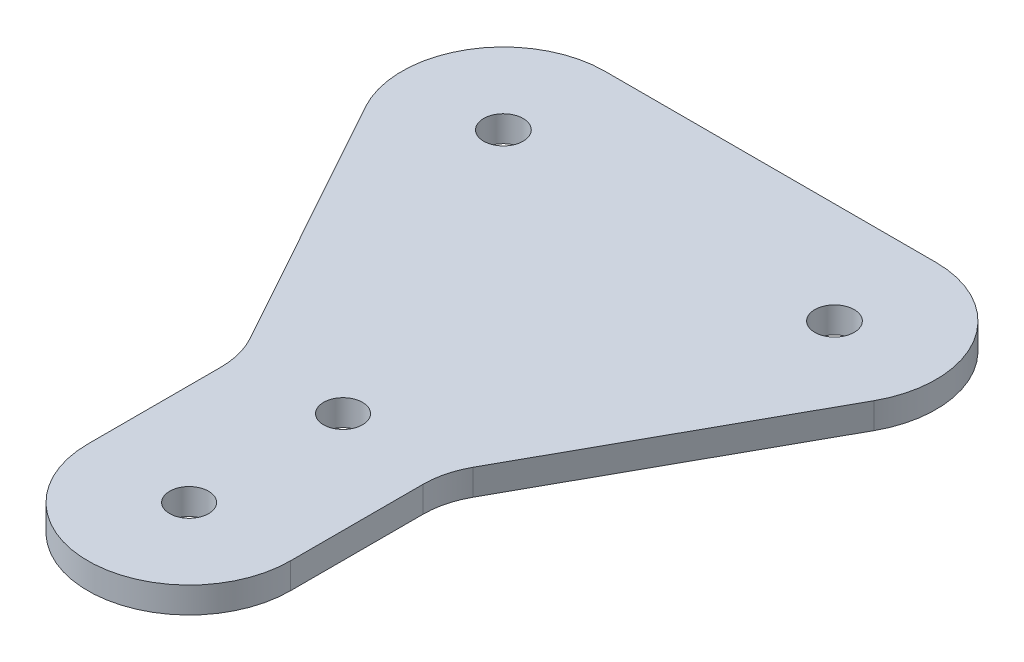
SolidWorks part; units mm, degrees
ref_plane "Front Plane" through (0, 0, 0) normal (0, 0, 1) x (1, 0, 0)
ref_plane "Top Plane" through (0, 0, 0) normal (0, 1, 0) x (1, 0, 0)
ref_plane "Right Plane" through (0, 0, 0) normal (1, 0, 0) x (0, 0, -1)
sketch "Sketch1" plane through (0, 0, 0) normal (0, 1, 0) x (1, 0, 0)
  line L0 (-12.3813, -29.3529) -> (-12.3813, -10.5324)
  line L1 (-12.3813, -10.5324) -> (-31.1054, 23.3121)
  line L2 (-20.2438, 41.7341) -> (20.2438, 41.7341)
  line L3 (31.1054, 23.3121) -> (12.3812, -10.5324)
  line L4 (12.3812, -10.5324) -> (12.3812, -29.3529)
  circle A0 centre (0, -29.3529) radius 2.3813
  circle A1 centre (20.2438, 29.3211) radius 2.413
  circle A2 centre (-20.2438, 29.3211) radius 2.413
  circle A3 centre (-20.2438, 29.3211) radius 12.413
  circle A4 centre (20.2438, 29.3211) radius 12.413
  circle A5 centre (0, -29.3529) radius 12.3813
  ellipse E0 centre (0, -10.5324) end of major axis (2.3813, -10.5324) minor radius 2.3812
  spline S0 degree 3 poles (11.7366, -15.3939) (12.7036, -10.5324) (11.7366, -5.6709) (8.9827, -1.5496) (4.8614, 1.2041) (0, 2.1711) (-4.8614, 1.2041) (-8.9827, -1.5496) (-11.5071, -5.3275) (-12.4011, -8.9039) (-12.4011, -12.1609) (-11.5071, -15.7374) (-8.9827, -19.5152) (-4.8614, -22.269) (0, -23.236) (4.8614, -22.269) (8.9827, -19.5152) (11.7366, -15.3939) (12.7036, -10.5324) (11.7366, -5.6709) knots -1.178097 -0.785398 -0.392699 0 0.392699 0.785398 1.178097 1.570796 1.963495 2.356194 2.748894 3.043418 3.239767 3.534292 3.926991 4.31969 4.712389 5.105088 5.497787 5.890486 6.283185 6.675884 7.068583 7.461283 only from (12.3812, -10.5324) to (12.3812, -10.5324)
  point P27 (0, 0)
extrude "Boss-Extrude1" add sketch "Sketch1" along normal blind 3.175 contours S0 A5 A0 | S0 L0 A5 | A5 S0 | S0 A5 L4 | S0 A5 E0 | S0 L3 A4 L2 A3 L1 | A4 A1 | A3 A2
fillet "Fillet1" radius 10 2 edges at (-12.3813, 1.5875, 10.5324) (12.3812, 1.5875, 10.5324)
